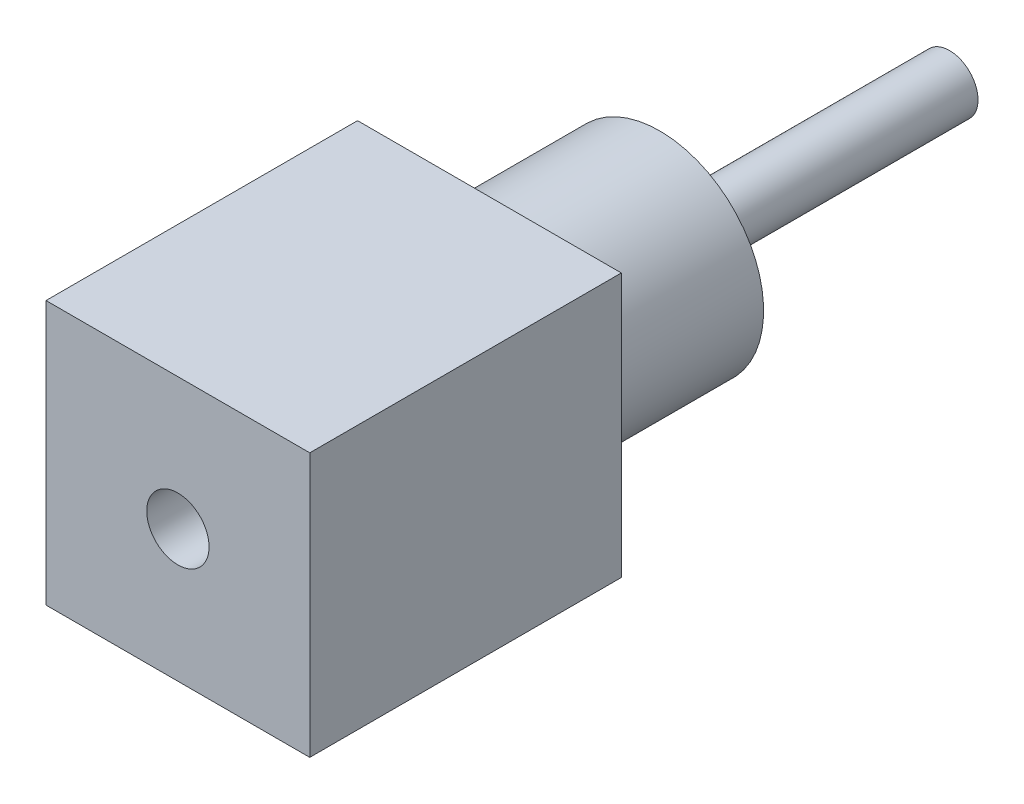
SolidWorks part; units mm, degrees
ref_plane "Front Plane" through (0, 0, 0) normal (0, 0, 1) x (1, 0, 0)
ref_plane "Top Plane" through (0, 0, 0) normal (0, 1, 0) x (1, 0, 0)
ref_plane "Right Plane" through (0, 0, 0) normal (1, 0, 0) x (0, 0, -1)
sketch "Sketch1" plane through (0, 0, 0) normal (0, 0, 1) x (1, 0, 0)
  line L1 (1.27, -1.27) -> (-1.27, -1.27)
  line L2 (1.27, -1.27) -> (1.27, 1.27)
  line L3 (1.27, 1.27) -> (-1.27, 1.27)
  line L4 (-1.27, -1.27) -> (-1.27, 1.27)
  line L5 (1.27, -1.27) -> (-1.27, 1.27) construction
  line L6 (1.27, 1.27) -> (-1.27, -1.27) construction
  point P0 (0, 0)
  dimension "D1" = 2.54
extrude "Boss-Extrude1" add sketch "Sketch1" along normal blind 3
sketch "Sketch2" plane through (0, 0, 0) normal (0, 0, -1) x (-1, 0, 0)
  circle A0 centre (0, 0) radius 1
  dimension "D1" = 2
extrude "Boss-Extrude2" add sketch "Sketch2" along normal blind 1.64
sketch "Sketch3" plane through (0, 0, -1.64) normal (0, 0, -1) x (-1, 0, 0)
  circle A0 centre (0, 0) radius 0.275
  dimension "D1" = 0.55
extrude "Boss-Extrude3" add sketch "Sketch3" along normal blind 2.79
sketch "Sketch4" plane through (0, 0, 3) normal (0, 0, 1) x (1, 0, 0)
  circle A0 centre (0, 0) radius 0.3
  dimension "D1" = 0.6
extrude "Cut-Extrude1" cut sketch "Sketch4" against normal blind 3
